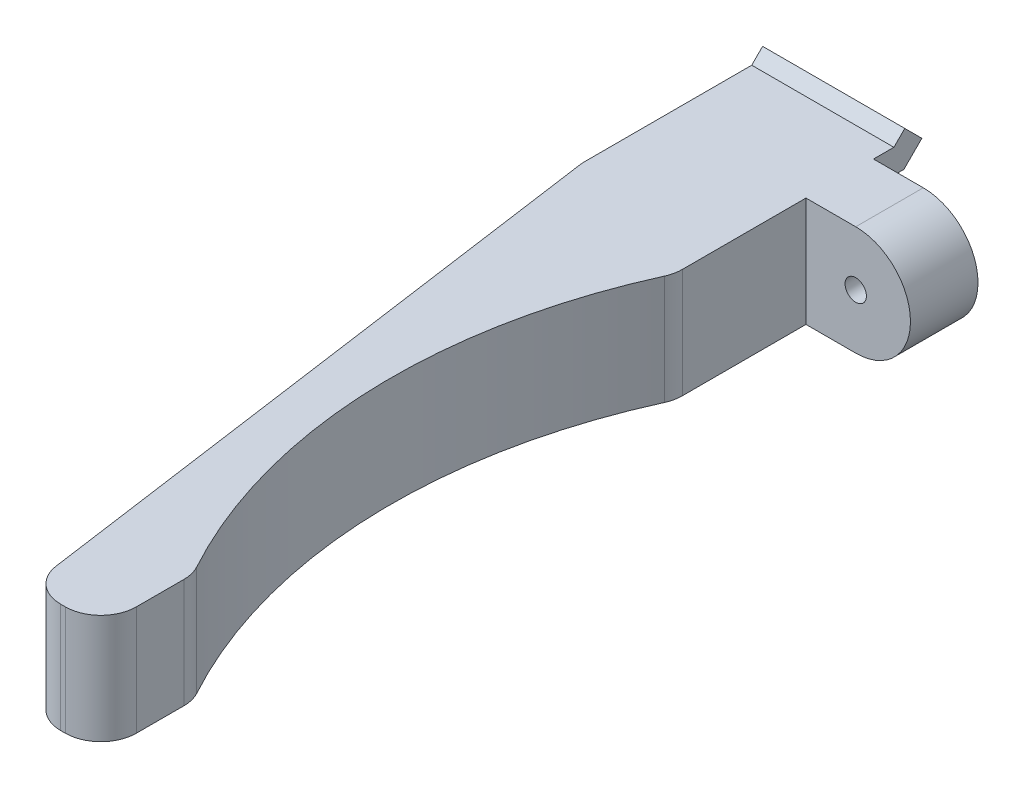
SolidWorks part; units mm, degrees
ref_plane "Front Plane" through (0, 0, 0) normal (0, 0, 1) x (1, 0, 0)
ref_plane "Top Plane" through (0, 0, 0) normal (0, 1, 0) x (1, 0, 0)
ref_plane "Right Plane" through (0, 0, 0) normal (1, 0, 0) x (0, 0, -1)
sketch "Sketch2" plane through (0, 0, 0) normal (0, 0, 1) x (1, 0, 0)
  line L0 (0, 5.9203) -> (0, 8.9503) construction
  line L1 (-5, -5.8182) -> (5, -5.8182)
  line L2 (-5, -5.8182) -> (-5, 8.9503)
  line L3 (-5, 8.9503) -> (5, 8.9503)
  line L4 (5, -5.8182) -> (5, 8.9503)
  line L5 (-26.3166, 8.9503) -> (11.3834, 8.9503) construction
  line L7 (5.6834, 5.9203) -> (-25.9417, 5.9203) construction
  line L8 (0, -5.8182) -> (0, -2.7882) construction
  point P0 (0, 0)
  dimension "D1" = 10
extrude "Boss-Extrude1" add sketch "Sketch2" along normal blind 5
sketch "Sketch8" plane through (-5, 0, 0) normal (-1, 0, 0) x (0, 0, 1)
  line L6 (-0.15, 5.7703) -> (0, 5.7703)
  line L7 (0, 8.9503) -> (0, -5.8182) construction
  line L8 (0, 5.7703) -> (0, 4.0703)
  line L9 (0, 4.0703) -> (-0.15, 4.0703)
  line L11 (-0.15, -1.9297) -> (0, -1.9297)
  line L12 (-2.1379, 4.0703) -> (-0.15, 4.0703)
  line L13 (-0.15, 4.0703) -> (-0.15, 5.7703)
  line L14 (-0.15, 5.7703) -> (-1.4337, 5.7703)
  line L15 (-1.4337, 5.7703) -> (-2.2, 6.5366)
  line L16 (-2.2, 6.5366) -> (-3.4021, 5.3345)
  line L17 (-3.4021, 5.3345) -> (-2.1379, 4.0703)
  line L18 (-2.1379, 4.0703) -> (-0.15, 4.0703)
  line L20 (-0.15, 5.7703) -> (-1.4337, 5.7703)
  line L21 (-1.4337, 5.7703) -> (-2.2, 6.5366)
  line L22 (-2.2, 6.5366) -> (-3.4021, 5.3345)
  line L23 (-3.4021, 5.3345) -> (-2.1379, 4.0703)
  line L24 (-2.1379, -1.9297) -> (-0.15, -1.9297)
  line L25 (-0.15, -1.9297) -> (-0.15, -0.2297)
  line L26 (-0.15, -0.2297) -> (-1.4337, -0.2297)
  line L27 (-1.4337, -0.2297) -> (-2.2, 0.5366)
  line L28 (-2.2, 0.5366) -> (-3.4021, -0.6655)
  line L29 (-3.4021, -0.6655) -> (-2.1379, -1.9297)
  line L30 (-2.1379, -1.9297) -> (-0.15, -1.9297)
  line L32 (-0.15, -0.2297) -> (-1.4337, -0.2297)
  line L33 (-1.4337, -0.2297) -> (-2.2, 0.5366)
  line L34 (-2.2, 0.5366) -> (-3.4021, -0.6655)
  line L35 (-3.4021, -0.6655) -> (-2.1379, -1.9297)
  line L37 (-0.15, -0.2297) -> (0, -0.2297)
  line L38 (0, -1.9297) -> (0, -0.2297)
  dimension "D1" = 0.15
  dimension "D2" = 0.15
extrude "Boss-Extrude4" add sketch "Sketch8" against normal up to surface (10 mm away) up to face at (5, 1.566, 2.5)
sketch "Sketch9" plane through (0, 0, 0) normal (0, 0, -1) x (-1, 0, 0)
  line L4 (-5, 8.9503) -> (-5, 5.7703)
  line L5 (-5, 5.7703) -> (5, 5.7703)
  line L6 (5, 5.7703) -> (5, 8.9503)
  line L7 (5, 8.9503) -> (-5, 8.9503)
  line L8 (-5, 8.9503) -> (-5, 5.7703)
  line L10 (5, 5.7703) -> (5, 8.9503)
  line L11 (5, 8.9503) -> (-5, 8.9503)
  line L16 (5, -1.9297) -> (-5, -1.9297)
  line L17 (-5, -1.9297) -> (-5, -5.8182)
  line L18 (-5, -5.8182) -> (5, -5.8182)
  line L19 (5, -5.8182) -> (5, -1.9297)
  line L21 (-5, -1.9297) -> (-5, -5.8182)
  line L22 (-5, -5.8182) -> (5, -5.8182)
  line L23 (5, -5.8182) -> (5, -1.9297)
  line L26 (-5, 5.7703) -> (5, 5.7703)
  line L27 (5, -1.9297) -> (-5, -1.9297)
  dimension "D1" = 0
  dimension "D2" = 0
extrude "Cut-Extrude3" cut sketch "Sketch9" against normal blind 5
sketch "Sketch10" plane through (0, 5.7703, 0) normal (0, 1, 0) x (1, 0, 0)
  line L0 (-5, -5) -> (-5, -10.5)
  line L1 (-5, -10.5) -> (1.3524, -55.7)
  line L2 (1.3524, -55.7) -> (6.3524, -55.7)
  line L3 (-5, -5) -> (5, -5)
  line L4 (-120.9789, 453.7107) -> (412.3545, 453.7107) construction
  line L5 (6.3524, -55.7) -> (6.3524, -49.2)
  line L6 (5, -5) -> (5, -14)
  arc A1 (5, -14) -> (6.3524, -49.2) centre (39.6089, -30.2962) ccw
  dimension "D1" = 172
  dimension "D7" = 38.2537
  dimension "D2" = 45.2
  dimension "D3" = 5
  dimension "D4" = 6.5
  dimension "D5" = 5.5
  dimension "D6" = 9
extrude "Boss-Extrude5" add sketch "Sketch10" against normal up to surface (7.7 mm away) up to face at (0, -1.9297, 1.4311)
ref_plane "Plane1" through (0, 0, 2.75) normal (0, 0, 1) x (1, 0, 0)
sketch "Sketch12" plane through (0, 0, 0) normal (0, 0, 1) x (1, 0, 0)
  line L0 (5, 5.7703) -> (8.5, 5.7703)
  line L1 (8.5, -1.9297) -> (5, -1.9297)
  line L2 (5, -1.9297) -> (5, 5.7703)
  line L3 (1.3524, 5.7703) -> (6.3524, 5.7703) construction
  line L4 (1.3524, -1.9297) -> (6.3524, -1.9297) construction
  line L5 (5, 5.3345) -> (5, 6.5366) construction
  line L6 (6.3524, 5.7703) -> (1.3552, 5.7703) construction
  arc A0 (8.5, 5.7703) -> (8.5, -1.9297) centre (8.5, 1.9203) cw
  circle A1 centre (8.5, 1.9203) radius 0.75
  dimension "D1" = 1.5
  dimension "D2" = 3.5
extrude "Boss-Extrude7" add sketch "Sketch12" along normal offset from surface (4.75 mm away) 2 up to plane "Plane1" offset beyond the face yes
fillet "Fillet1" radius 2.5 4 edges at (6.3524, 1.9203, 55.7) (1.3524, 1.9203, 55.7) (6.3524, 1.9203, 49.2) (5, 1.9203, 14)
